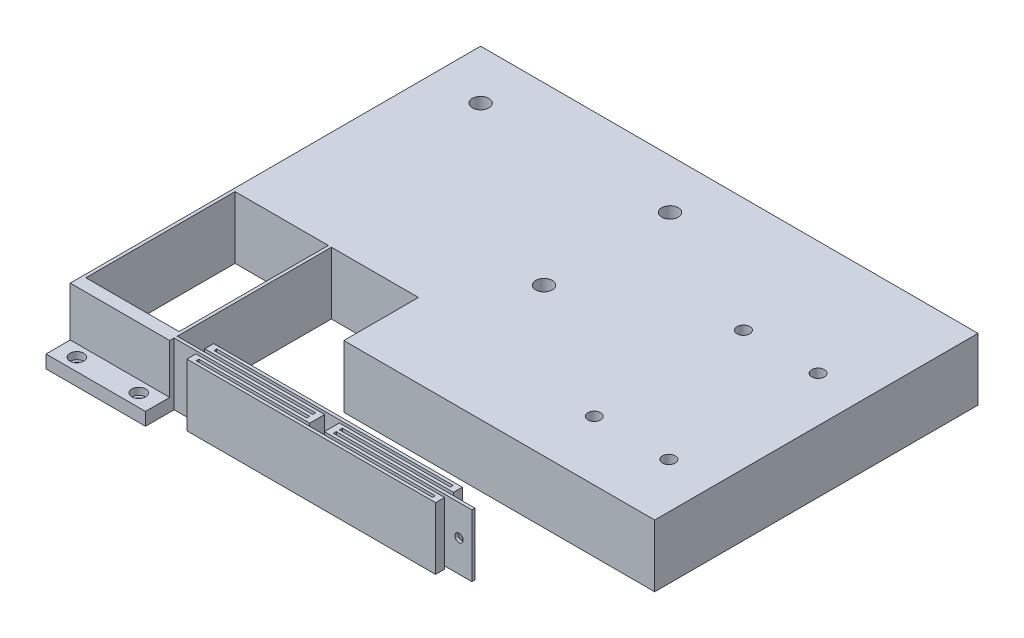
SolidWorks part; units mm, degrees
material "2024-O"
ref_plane "Front Plane" through (0, 0, 0) normal (0, 0, 1) x (1, 0, 0)
ref_plane "Top Plane" through (0, 0, 0) normal (0, 1, 0) x (1, 0, 0)
ref_plane "Right Plane" through (0, 0, 0) normal (1, 0, 0) x (0, 0, -1)
sketch "Sketch1" plane through (0, 0, 0) normal (0, 1, 0) x (1, 0, 0)
  line L1 (-100, 87.375) -> (100, 87.375)
  line L2 (-100, 87.375) -> (-100, -87.375)
  line L3 (-100, -87.375) -> (100, -87.375)
  line L4 (100, 87.375) -> (100, -87.375)
  point P4 (100, 0)
  point P6 (0, 87.375)
  dimension "D1" = 200
  dimension "D2" = 174.75
extrude "Boss-Extrude1" add sketch "Sketch1" along normal blind 25
sketch "Sketch2" plane through (0, 25, 0) normal (0, 1, 0) x (1, 0, 0)
  line L0 (-100, 87.375) -> (-100, -87.375) construction
  line L1 (-100, -77.625) -> (-60, -77.625)
  line L2 (-100, -77.625) -> (-100, -87.375)
  line L3 (-100, -87.375) -> (-60, -87.375)
  line L4 (-60, -77.625) -> (-60, -87.375)
  line L5 (-100, -87.375) -> (100, -87.375) construction
  dimension "D1" = 40
  dimension "D2" = 9.75
extrude "Cut-Extrude1" cut sketch "Sketch2" against normal offset from surface (19.8 mm away) 5.2 up to face at (0, 0, 0)
sketch "Sketch3" plane through (0, 25, 0) normal (0, 1, 0) x (1, 0, 0)
  line L0 (-100, 87.375) -> (-100, -77.625) construction
  line L1 (-98.73, -12.625) -> (-61.23, -12.625)
  line L2 (-98.73, -12.625) -> (-98.73, -72.625)
  line L3 (-98.73, -72.625) -> (-61.23, -72.625)
  line L4 (-61.23, -12.625) -> (-61.23, -72.625)
  line L5 (-100, -77.625) -> (-60, -77.625) construction
  line L6 (-25, -42.625) -> (100, -42.625)
  line L7 (-25, -12.625) -> (-60, -12.625)
  line L8 (-25, -12.625) -> (-25, -42.625)
  line L10 (-60, -12.625) -> (-60, -87.375)
  line L13 (100, -87.375) -> (100, 87.375) construction
  line L14 (100, 87.375) -> (-100, 87.375) construction
  line L15 (-60, -87.375) -> (-60, -77.625) construction
  line L16 (-60, -87.375) -> (100, -87.375) construction
  line L17 (-60, -87.375) -> (100, -87.375)
  line L18 (100, -87.375) -> (100, -42.625)
  dimension "D1" = 1.27
  dimension "D2" = 5
  dimension "D3" = 37.5
  dimension "D4" = 60
  dimension "D5" = 35
  dimension "D9" = 130
extrude "Cut-Extrude2" cut sketch "Sketch3" against normal through all
sketch "Sketch4" plane through (0, 25, 0) normal (0, 1, 0) x (1, 0, 0)
  line L0 (-60, -12.625) -> (-60, -77.625) construction
  line L1 (-60, -74.625) -> (-5.5, -74.625)
  line L2 (-60, -74.625) -> (-60, -75.855)
  line L3 (-60, -75.855) -> (-5.5, -75.855)
  line L5 (-25, -12.625) -> (-60, -12.625) construction
  line L28 (-5.5, -74.625) -> (-5.5, -73.455)
  line L29 (-5.5, -73.455) -> (-50.1, -73.455)
  line L30 (-50.1, -73.455) -> (-50.1, -69.865)
  line L31 (-50.1, -69.865) -> (49.9, -69.865)
  line L32 (49.9, -69.865) -> (49.9, -73.455)
  line L33 (49.9, -73.455) -> (5.2, -73.455)
  line L34 (5.2, -73.455) -> (5.2, -74.625)
  line L35 (5.2, -74.625) -> (59.7, -74.625)
  line L36 (59.7, -74.625) -> (59.7, -75.855)
  line L37 (59.7, -75.855) -> (5.2, -75.855)
  line L38 (5.2, -75.855) -> (5.2, -77.025)
  line L39 (5.2, -77.025) -> (49.9, -77.025)
  line L40 (49.9, -77.025) -> (49.9, -80.615)
  line L41 (49.9, -80.615) -> (-50.1, -80.615)
  line L42 (-50.1, -80.615) -> (-50.1, -77.025)
  line L43 (-50.1, -77.025) -> (-5.5, -77.025)
  line L44 (-5.5, -77.025) -> (-5.5, -75.855)
  line L45 (-3.1, -72.225) -> (-3.1, -78.255)
  line L46 (-3.1, -78.255) -> (-47.63, -78.255)
  line L47 (-47.63, -78.255) -> (-47.63, -79.385)
  line L48 (-47.63, -79.385) -> (47.43, -79.385)
  line L49 (47.43, -79.385) -> (47.43, -78.255)
  line L50 (47.43, -78.255) -> (2.8, -78.255)
  line L51 (2.8, -78.255) -> (2.8, -72.225)
  line L52 (2.8, -72.225) -> (47.43, -72.225)
  line L53 (47.43, -72.225) -> (47.43, -71.095)
  line L54 (47.43, -71.095) -> (-47.63, -71.095)
  line L55 (-47.63, -71.095) -> (-47.63, -72.225)
  line L56 (-47.63, -72.225) -> (-3.1, -72.225)
  line L58 (-60, -12.625) -> (-60, -77.625) construction
  dimension "D1" = 1.23
  dimension "D2" = 1.23
  dimension "D3" = 1.23
  dimension "D4" = 2.47
  dimension "D5" = 2.4
  dimension "D6" = 100
  dimension "D7" = 5.9
  dimension "D8" = 2.4
  dimension "D9" = 2.47
  dimension "D10" = 10.75
  dimension "D11" = 1.23
  dimension "D12" = 54.5
  dimension "D13" = 62
  dimension "D14" = 1.17
  dimension "D15" = 9.9
extrude "Boss-Extrude2" add sketch "Sketch4" against normal up to surface (25 mm away) up to face at (-79.98, 0, 42.625)
sketch "Sketch5" plane through (0, 0, 75.855) normal (0, 0, 1) x (1, 0, 0)
  line L0 (59.7, 0) -> (5.2, 0) construction
  line L1 (59.7, 0) -> (59.7, 25) construction
  circle A0 centre (54.55, 12.65) radius 1.65
  dimension "D1" = 3.3
  dimension "D3" = 3.5
  dimension "D2" = 11
extrude "Cut-Extrude3" cut sketch "Sketch5" against normal up to surface (1.23 mm away) up to face at (32.45, 12.5, 74.625)
sketch "Sketch6" plane through (0, 25, 0) normal (0, 1, 0) x (1, 0, 0)
  line L0 (-100, 87.375) -> (-100, -77.625) construction
  line L1 (100, 87.375) -> (-100, 87.375) construction
  circle A0 centre (-80.175, 67.55) radius 3.325
  circle A1 centre (-4.025, 67.55) radius 3.325
  circle A2 centre (-4.025, 16.9) radius 3.325
  dimension "D1" = 6.65
  dimension "D2" = 69.5
  dimension "D3" = 44
  dimension "D4" = 16.5
  dimension "D5" = 16.5
extrude "Cut-Extrude4" cut sketch "Sketch6" against normal through all
sketch "Sketch7" plane through (0, 5.2, 0) normal (0, 1, 0) x (1, 0, 0)
  line L0 (-60, -87.375) -> (-100, -87.375) construction
  line L1 (-100, -87.375) -> (-100, -77.625) construction
  circle A0 centre (-92.665, -82.29) radius 0.685
  circle A1 centre (-67.795, -82.29) radius 0.685
  dimension "D1" = 1.37
  dimension "D4" = 23.5
  dimension "D2" = 4.4
  dimension "D3" = 6.65
extrude "Cut-Extrude5" cut sketch "Sketch7" against normal through all
hole_wizard "1/4-20 Tapped Hole1" positions "Sketch8" profile "Sketch9" tap size "1/4-20" standard "ANSI Inch" end condition through all
sketch "Sketch8" plane through (0, 25, 0) normal (0, 1, 0) x (1, 0, 0)
  line L0 (100, -42.625) -> (100, 87.375) construction
  line L2 (100, -42.625) -> (-25, -42.625) construction
  point P0 (51.7452, 41.3269)
  point P3 (81.7485, 41.3269)
  point P6 (81.7485, -18.6731)
  point P9 (51.7452, -18.6731)
  dimension "D4" = 60
  dimension "D5" = 30.0033
  dimension "D6" = 23.9519
  dimension "D7" = 18.2515
sketch "Sketch9" plane through (51.7452, 25, -41.3269) normal (1, 0, 0) x (0, 0, 1)
  line L0 (0, 0) -> (0, 25)
  line L1 (0, 25) -> (2.5527, 25)
  line L2 (2.5527, 25) -> (2.5527, 0)
  line L5 (2.5527, 0) -> (0, 0)
  line L11 (0, -6.35) -> (0, 107.95) construction
  dimension "Thru Tap Drill Dia." = 5.1054
  dimension "Thru Tap Drill Depth" = 25
cosmetic thread "Hole Thread1" parameters "D2"=6.35
cosmetic thread "Hole Thread2" parameters "D2"=6.35
cosmetic thread "Hole Thread3" parameters "D2"=6.35
cosmetic thread "Hole Thread4" parameters "D2"=6.35
hole_wizard "CBORE for #4 Socket Head Cap Screw1" positions "Sketch10" profile "Sketch11" counterbore size "#4" standard "ANSI Inch" end condition through all
sketch "Sketch10" plane through (0, 5.2, 0) normal (0, 1, 0) x (1, 0, 0)
  point P0 (-92.665, -82.29)
  point P3 (-67.795, -82.29)
sketch "Sketch11" plane through (-92.665, 5.2, 82.29) normal (1, 0, 0) x (0, 0, 1)
  line L0 (0, 0) -> (0, 5.2)
  line L1 (0, 5.2) -> (1.6319, 5.2)
  line L3 (1.6319, 5.2) -> (1.6319, 2.8448)
  line L4 (1.6319, 2.8448) -> (2.7788, 2.8448)
  line L5 (2.7788, 2.8448) -> (2.7788, 0)
  line L7 (2.7788, 0) -> (0, 0)
  line L11 (0, -6.35) -> (0, 107.95) construction
  dimension "Thru Hole Dia." = 3.2639
  dimension "Thru Hole Depth" = 5.2
  dimension "C'Bore Dia." = 5.5575
  dimension "C'Bore Depth" = 2.8448
